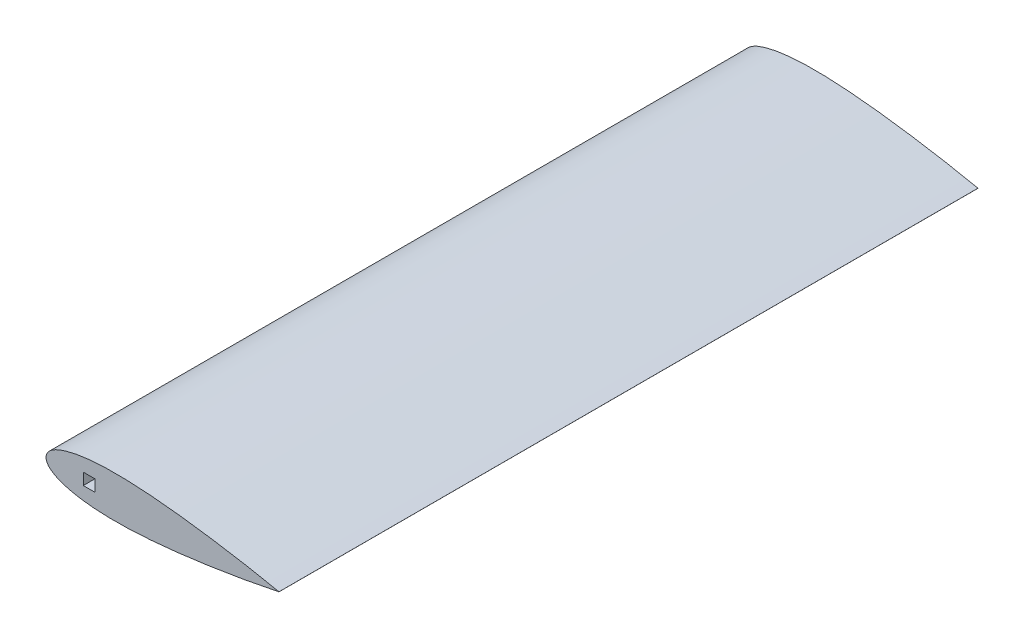
SolidWorks part; units mm, degrees
material "polystirene foam"
ref_plane "Front Plane" through (0, 0, 0) normal (0, 0, 1) x (1, 0, 0)
ref_plane "Top Plane" through (0, 0, 0) normal (0, 1, 0) x (1, 0, 0)
ref_plane "Right Plane" through (0, 0, 0) normal (1, 0, 0) x (0, 0, -1)
curve "Curve1"
  spline degree 3 poles (267.933, 0.5337, 0) (270.49, -0.1564, 0) (268.2375, 0.6665, 0) (266.5672, 1.4668, 0) (262.6756, 3.0154, 0) (257.9132, 4.5724, 0) (251.732, 6.3325, 0) (244.4112, 8.2376, 0) (235.9576, 10.2728, 0) (226.5142, 12.3893, 0) (216.1934, 14.5409, 0) (205.1313, 16.6775, 0) (193.4567, 18.7298, 0) (181.2977, 20.6324, 0) (168.7678, 22.3117, 0) (155.9753, 23.7079, 0) (143.0353, 24.8049, 0) (130.0617, 25.5802, 0) (117.1734, 26.0003, 0) (104.4837, 26.0576, 0) (92.1044, 25.7531, 0) (80.1395, 25.0742, 0) (68.69, 24.0381, 0) (57.8509, 22.6699, 0) (47.7143, 21.0125, 0) (38.3732, 19.0872, 0) (29.9084, 16.9558, 0) (22.399, 14.6444, 0) (15.9079, 12.2159, 0) (10.4843, 9.7202, 0) (6.177, 7.2209, 0) (2.9612, 4.7412, 0) (0.9766, 2.4261, 0) (0.0237, 0.7907, 0) (-0.0162, -0.4697, 0) (0.8003, -1.8361, 0) (3.4921, -2.6295, 0) (7.308, -3.6627, 0) (12.6566, -4.3991, 0) (19.3194, -5.0329, 0) (27.2905, -5.4698, 0) (36.4622, -5.7387, 0) (46.7414, -5.84, 0) (58.0105, -5.7702, 0) (70.1434, -5.5368, 0) (83.0071, -5.1408, 0) (96.4629, -4.5659, 0) (110.374, -3.827, 0) (124.6167, -2.893, 0) (139.0995, -1.7363, 0) (153.7348, -0.4008, 0) (168.4097, 0.8923, 0) (182.9339, 2.0414, 0) (197.0782, 2.9592, 0) (210.6044, 3.579, 0) (223.2667, 3.8744, 0) (234.8405, 3.8186, 0) (245.0477, 3.4533, 0) (253.7786, 2.7629, 0) (260.4407, 1.9422, 0) (265.7815, 0.9299, 0) (267.933, 0.5337, 0) (270.49, -0.1564, 0) (268.2375, 0.6665, 0) knots -0.016249 -0.007187 -0.001789 0 0.001694 0.006395 0.013462 0.022754 0.034367 0.048191 0.064031 0.081681 0.100894 0.121432 0.143025 0.165434 0.188439 0.211855 0.235496 0.259144 0.282615 0.305702 0.328232 0.35003 0.370944 0.390817 0.409506 0.426857 0.442733 0.457018 0.469615 0.48045 0.489472 0.49673 0.502329 0.506256 0.506442 0.509182 0.513914 0.521178 0.530944 0.543145 0.55767 0.574384 0.59311 0.613638 0.635744 0.659184 0.683714 0.709076 0.735036 0.76143 0.788184 0.815057 0.841645 0.867514 0.892232 0.915364 0.936485 0.9552 0.971104 0.983751 0.992813 0.998211 1 1.001694 1.006395 1.013462 periodic
curve "Curve2"
  spline degree 3 poles (1, 0.0019, 0) (0.9833, 0.0053, 0) (0.9501, 0.0122, 0) (0.8834, 0.025, 0) (0.8002, 0.0397, 0) (0.7001, 0.0553, 0) (0.6002, 0.0688, 0) (0.5002, 0.0799, 0) (0.4001, 0.0878, 0) (0.3167, 0.0906, 0) (0.25, 0.0895, 0) (0.1999, 0.0865, 0) (0.1497, 0.0808, 0) (0.1079, 0.0728, 0) (0.0746, 0.0633, 0) (0.0492, 0.0537, 0) (0.0279, 0.0421, 0) (0.0083, 0.0261, 0) (-0.0054, 0, 0) (0.0083, -0.0261, 0) (0.0279, -0.0421, 0) (0.0492, -0.0537, 0) (0.0746, -0.0633, 0) (0.1079, -0.0728, 0) (0.1497, -0.0808, 0) (0.1999, -0.0865, 0) (0.25, -0.0895, 0) (0.3167, -0.0906, 0) (0.4001, -0.0878, 0) (0.5002, -0.0799, 0) (0.6002, -0.0688, 0) (0.7001, -0.0553, 0) (0.8002, -0.0397, 0) (0.8834, -0.025, 0) (0.9501, -0.0122, 0) (0.9833, -0.0053, 0) (1, -0.0019, 0) knots 0 0 0 0 0.024604 0.049152 0.098109 0.146905 0.195555 0.244056 0.29241 0.340644 0.364754 0.388906 0.413178 0.437756 0.450305 0.46323 0.477068 0.485036 0.5 0.514964 0.522932 0.53677 0.549695 0.562244 0.586822 0.611094 0.635246 0.659356 0.70759 0.755944 0.804445 0.853095 0.901891 0.950848 0.975396 1 1 1 1
sketch "Sketch2" plane through (0, 0, 0) normal (0, 0, 1) x (1, 0, 0)
  line L1 (0, 0) -> (200, 0) construction
  line L2 (0, 5.3617) -> (0, 0) construction
  line L3 (200, 0.026) -> (200, -0.026)
  line L4 (0, 17.8541) -> (200, 17.8541) construction
  line L5 (0, -17.8541) -> (200, -17.8541) construction
  spline S1 degree 3 poles (200, 0.026) (196.1337, 0.8245) (188.9731, 2.314) (175.1972, 4.9535) (158.6821, 7.8644) (138.8483, 10.963) (119.0176, 13.6524) (99.1866, 15.8519) (79.3508, 17.4108) (62.8016, 17.9646) (49.5701, 17.7436) (39.6384, 17.1555) (29.688, 16.02) (21.4064, 14.4333) (14.8011, 12.5462) (9.7569, 10.6396) (5.5318, 8.3438) (1.6454, 5.1683) (-1.0737, 0) (1.6454, -5.1683) (5.5318, -8.3438) (9.7569, -10.6396) (14.8011, -12.5462) (21.4064, -14.4333) (29.688, -16.02) (39.6384, -17.1555) (49.5701, -17.7436) (62.8016, -17.9646) (79.3508, -17.4108) (99.1866, -15.8519) (119.0176, -13.6524) (138.8483, -10.963) (158.6821, -7.8644) (175.1972, -4.9535) (188.9731, -2.314) (196.1337, -0.8245) (200, -0.026) knots -0.00419 -0.00419 -0.00419 -0.00419 0.024604 0.049152 0.098109 0.146905 0.195555 0.244056 0.29241 0.340644 0.364754 0.388906 0.413178 0.437756 0.450305 0.46323 0.477068 0.485036 0.5 0.514964 0.522932 0.53677 0.549695 0.562244 0.586822 0.611094 0.635246 0.659356 0.70759 0.755944 0.804445 0.853095 0.901891 0.950848 0.975396 1.00419 1.00419 1.00419 1.00419
  dimension "D1" = 200
extrude "Boss-Extrude1" add sketch "Sketch2" along normal blind 600 contours S1 L3
sketch "Sketch3" plane through (0, 0, 600) normal (0, 0, 1) x (1, 0, 0)
  line L0 (0, 0) -> (20, 0)
  line L1 (0, 0) -> (200, 0) construction
  line L2 (20, 0) -> (30, 0)
  line L3 (30, 0) -> (30, -24.2417)
  line L4 (20, 0) -> (20, -24.2417)
  line L5 (20, -24.2417) -> (30, -24.2417)
  line L6 (30, 0) -> (20, 0)
  line L7 (20, 0) -> (20, -24.2417)
  line L8 (20, -24.2417) -> (30, -24.2417)
  line L9 (30, -24.2417) -> (30, 0)
sketch "Sketch5" plane through (0, 0, 0) normal (0, 0, -1) x (-1, 0, 0)
  line L0 (0, 0) -> (-18, 0)
  line L1 (0, 0) -> (-200, 0) construction
  line L2 (-18, 0) -> (-18, 13.4428)
  spline S0 degree 3 poles (-200, 0.026) (-196.1337, 0.8245) (-188.9731, 2.314) (-175.1972, 4.9535) (-158.6821, 7.8644) (-138.8483, 10.963) (-119.0176, 13.6524) (-99.1866, 15.8519) (-79.3508, 17.4108) (-62.8016, 17.9646) (-49.5701, 17.7436) (-39.6384, 17.1555) (-29.688, 16.02) (-21.4064, 14.4333) (-14.8011, 12.5462) (-9.7569, 10.6396) (-5.5318, 8.3438) (-1.6454, 5.1683) (1.0737, 0) (-1.6454, -5.1683) (-5.5318, -8.3438) (-9.7569, -10.6396) (-14.8011, -12.5462) (-21.4064, -14.4333) (-29.688, -16.02) (-39.6384, -17.1555) (-49.5701, -17.7436) (-62.8016, -17.9646) (-79.3508, -17.4108) (-99.1866, -15.8519) (-119.0176, -13.6524) (-138.8483, -10.963) (-158.6821, -7.8644) (-175.1972, -4.9535) (-188.9731, -2.314) (-196.1337, -0.8245) (-200, -0.026) knots -0.00419 -0.00419 -0.00419 -0.00419 0.024604 0.049152 0.098109 0.146905 0.195555 0.244056 0.29241 0.340644 0.364754 0.388906 0.413178 0.437756 0.450305 0.46323 0.477068 0.485036 0.5 0.514964 0.522932 0.53677 0.549695 0.562244 0.586822 0.611094 0.635246 0.659356 0.70759 0.755944 0.804445 0.853095 0.901891 0.950848 0.975396 1.00419 1.00419 1.00419 1.00419 construction
sketch "Sketch6" plane through (0, 0, 600) normal (0, 0, 1) x (1, 0, 0)
  line L0 (30, 0) -> (20, 0)
  line L1 (20, 0) -> (18, 0)
  line L2 (30, 0) -> (32, 0)
  line L3 (0, 0) -> (200, 0) construction
  line L4 (18, 0) -> (18, -22.0484)
  line L5 (18, -22.0484) -> (18, -25.4056)
  line L6 (32, 0) -> (32, -25.4056)
  line L7 (18, -25.4056) -> (32, -25.4056)
  line L8 (30, 0) -> (30, -24.2417) construction
  line L9 (20, 5) -> (30, 5)
  line L10 (20, 5) -> (20, -5)
  line L11 (20, -5) -> (30, -5)
  line L12 (30, 5) -> (30, -5)
  line L13 (20, 5) -> (30, -5) construction
  line L14 (20, -5) -> (30, 5) construction
  point P12 (25, 0)
  dimension "D1" = 10
extrude "Cut-Extrude2" cut sketch "Sketch6" against normal blind 656 contours L12 L9 L10 L0 | L12 L0 L10 L11
sketch "Sketch8" plane through (0, 5, 0) normal (0, -1, 0) x (-1, 0, 0)
  line L0 (-30, -600) -> (-30, 0)
  line L1 (-30, -300) -> (-30, -350)
  line L2 (-30, -300) -> (-30, -250)
  line L13 (-30, -350) -> (-32, -350)
  line L14 (-32, -350) -> (-32, -364)
  line L15 (-32, -364) -> (-18, -364)
  line L16 (-18, -364) -> (-18, -350)
  line L17 (-30, -350) -> (-18, -350)
  line L18 (-30, -250) -> (-18, -250)
  line L19 (-18, -250) -> (-18, -236)
  line L20 (-18, -236) -> (-32, -236)
  line L21 (-32, -236) -> (-32, -250)
  line L22 (-30, -250) -> (-32, -250)
  line M3 (-30, 0) -> (-30, -600)
  line M5 (-20, -600) -> (-20, 0)
extrude "Cut-Extrude4" cut sketch "Sketch8" against normal blind 2 and the other way blind 42 contours L20 L0 L18 M5 | L17 L15 M3 M5 | L17 L15 L16 M5 | L14 L15 L13 M3 | L19 L20 L18 M5 | L22 L0 L20 L21
sketch "Sketch9" plane through (32, 0, 0) normal (-1, 0, 0) x (0, 0, 1)
  line L1 (350, 7) -> (364, 7)
  line L2 (350, 7) -> (350, -7)
  line L3 (350, -7) -> (364, -7)
  line L4 (364, 7) -> (364, -7)
  dimension "D1" = 14
  dimension "D2" = 14
extrude "Cut-Extrude5" cut sketch "Sketch9" against normal blind 14
sketch "Sketch10" plane through (32, 0, 0) normal (-1, 0, 0) x (0, 0, 1)
  line L1 (236, 7) -> (250, 7)
  line L2 (236, 7) -> (236, -7)
  line L3 (236, -7) -> (250, -7)
  line L4 (250, 7) -> (250, -7)
  dimension "D1" = 14
  dimension "D2" = 14
extrude "Cut-Extrude6" cut sketch "Sketch10" against normal blind 14
sketch "Sketch11" plane through (0, 0, 600) normal (0, 0, 1) x (1, 0, 0)
  line L0 (30, 5) -> (32, 5)
  line L1 (32, 5) -> (42, 5)
  line L2 (32, 5) -> (32, -5)
  line L3 (32, -5) -> (42, -5)
  line L4 (42, -5) -> (42, 5)
extrude "Cut-Extrude7" cut sketch "Sketch11" against normal blind 654 contours L3 L4 L1 L2
sketch "Sketch12" plane through (0, 0, 600) normal (0, 0, 1) x (1, 0, 0)
  line L0 (30, 0) -> (30, -24.2417) construction
  line L1 (20, 5) -> (30, 5)
  line L2 (20, 5) -> (20, -5)
  line L3 (20, -5) -> (30, -5)
  line L4 (30, 5) -> (30, -5)
  line L5 (20, -5) -> (30, -5) construction
extrude "Boss-Extrude3" add sketch "Sketch12" against normal blind 600 contours L2 L1 L4 L3
sketch "Sketch13" plane through (0, -5, 0) normal (0, -1, 0) x (-1, 0, 0)
  line L0 (-32, -236) -> (-18, -236) construction
  line L1 (-20, -250) -> (-30, -250)
  line L2 (-20, -250) -> (-20, -236)
  line L3 (-20, -236) -> (-30, -236)
  line L4 (-30, -250) -> (-30, -236)
  line L5 (-18, -236) -> (-46, -236) construction
extrude "Cut-Extrude8" cut sketch "Sketch13" against normal blind 10
sketch "Sketch14" plane through (0, -5, 0) normal (0, -1, 0) x (-1, 0, 0)
  line L1 (-20, -364) -> (-30, -364)
  line L2 (-20, -364) -> (-20, -350)
  line L3 (-20, -350) -> (-30, -350)
  line L4 (-30, -364) -> (-30, -350)
extrude "Cut-Extrude9" cut sketch "Sketch14" against normal blind 10
sketch "Sketch15" plane through (46, 0, 0) normal (-1, 0, 0) x (0, 0, 1)
  line L0 (350, 7) -> (350, -7)
  line L1 (350, 7) -> (350, -7) construction
  line L2 (350, -7) -> (364, -7)
  line L3 (350, 7) -> (364, 7)
  line L4 (364, 7) -> (350, 7) construction
  line L5 (364, 7) -> (364, -7)
sketch "Sketch16" plane through (46, 0, 0) normal (-1, 0, 0) x (0, 0, 1)
  line L0 (350, -7) -> (350, -2.5)
  line L1 (350, -7) -> (364, -7)
  line L2 (364, -7) -> (364, -2.5)
  line L3 (364, -2.5) -> (350, -2.5)
  line L5 (350, -2.5) -> (364, -2.5)
  line L6 (350, -2.5) -> (350, -7)
  line L7 (350, -7) -> (364, -7)
  line L8 (364, -2.5) -> (364, -7)
  line M1 (350, 7) -> (350, -7)
  line M2 (350, -7) -> (364, -7)
  line M3 (364, -7) -> (364, 7)
extrude "Cut-Extrude10" cut sketch "Sketch16" against normal blind 10 contours L3 M3 M1 M2
sketch "Sketch17" plane through (46, 0, 0) normal (-1, 0, 0) x (0, 0, 1)
  line L0 (350, 7) -> (350, -7)
  line L1 (350, -7) -> (364, -7)
  line L2 (364, -7) -> (364, 2)
  line L3 (364, 2) -> (350, 2)
  line L4 (350, 2) -> (350, -7)
  line M1 (350, -2.5) -> (364, -2.5)
  line M2 (364, -2.5) -> (364, 7)
extrude "Cut-Extrude11" cut sketch "Sketch17" against normal blind 14 contours L3 L0 M2 M1
